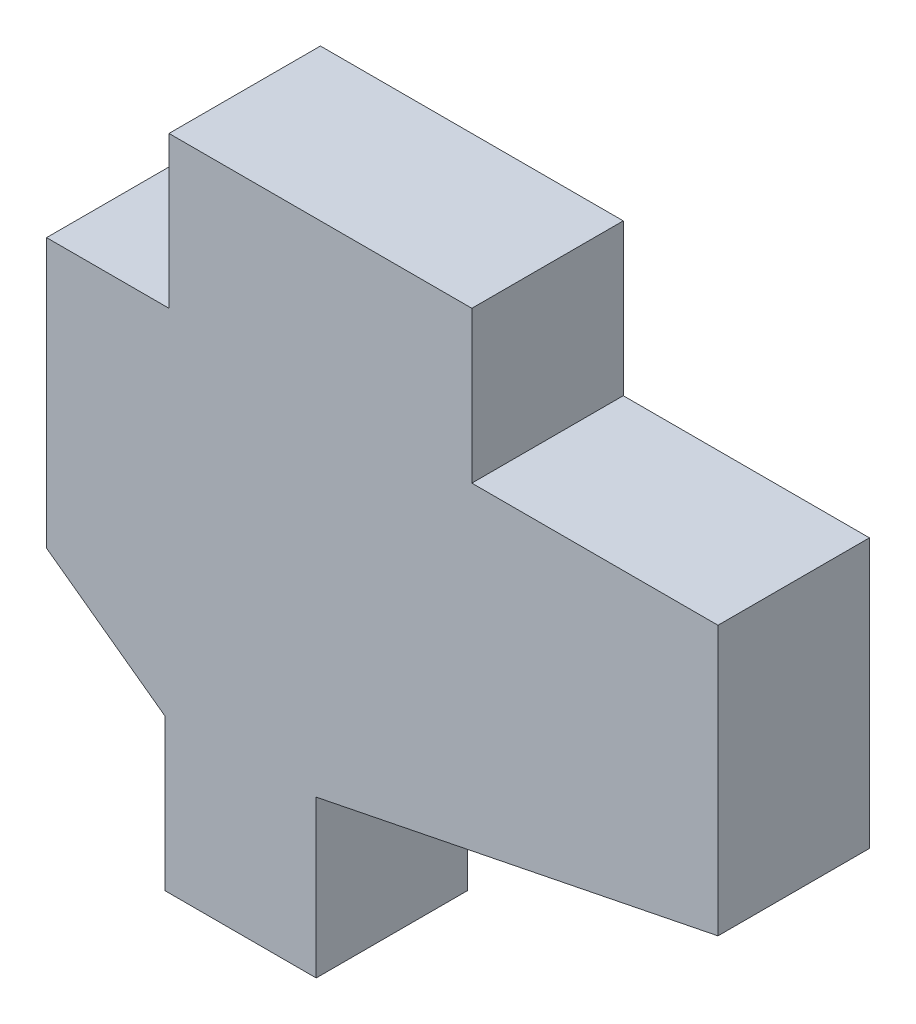
SolidWorks part; units mm, degrees
ref_plane "Front Plane" through (0, 0, 0) normal (0, 0, 1) x (1, 0, 0)
ref_plane "Top Plane" through (0, 0, 0) normal (0, 1, 0) x (1, 0, 0)
ref_plane "Right Plane" through (0, 0, 0) normal (1, 0, 0) x (0, 0, -1)
sketch "Sketch1" plane through (0, 0, 0) normal (0, 0, 1) x (1, 0, 0)
  line L0 (-75.1467, -1.524) -> (-75.1467, 0)
  line L1 (-75.1467, 0) -> (-72.0987, 0)
  line L2 (-72.0987, 0) -> (-72.0987, -1.524)
  line L3 (-72.0987, -1.524) -> (-69.6215, -1.524)
  line L4 (-69.6215, -1.524) -> (-69.6215, -4.2314)
  line L5 (-75.1467, -1.524) -> (-76.3786, -1.524)
  line L6 (-76.3786, -1.524) -> (-76.3786, -4.2314)
  line L7 (-76.3786, -4.2314) -> (-75.1892, -5.0964)
  line L9 (-73.6652, -5.0437) -> (-69.6215, -4.2314)
  line L10 (-75.1892, -5.0964) -> (-75.1892, -6.6204)
  line L11 (-75.1892, -6.6204) -> (-73.6652, -6.6204)
  line L12 (-73.6652, -6.6204) -> (-73.6652, -5.0437)
  dimension "D1" = 1.524
  dimension "D2" = 1.524
extrude "Boss-Extrude1" add sketch "Sketch1" along normal blind 1.524
